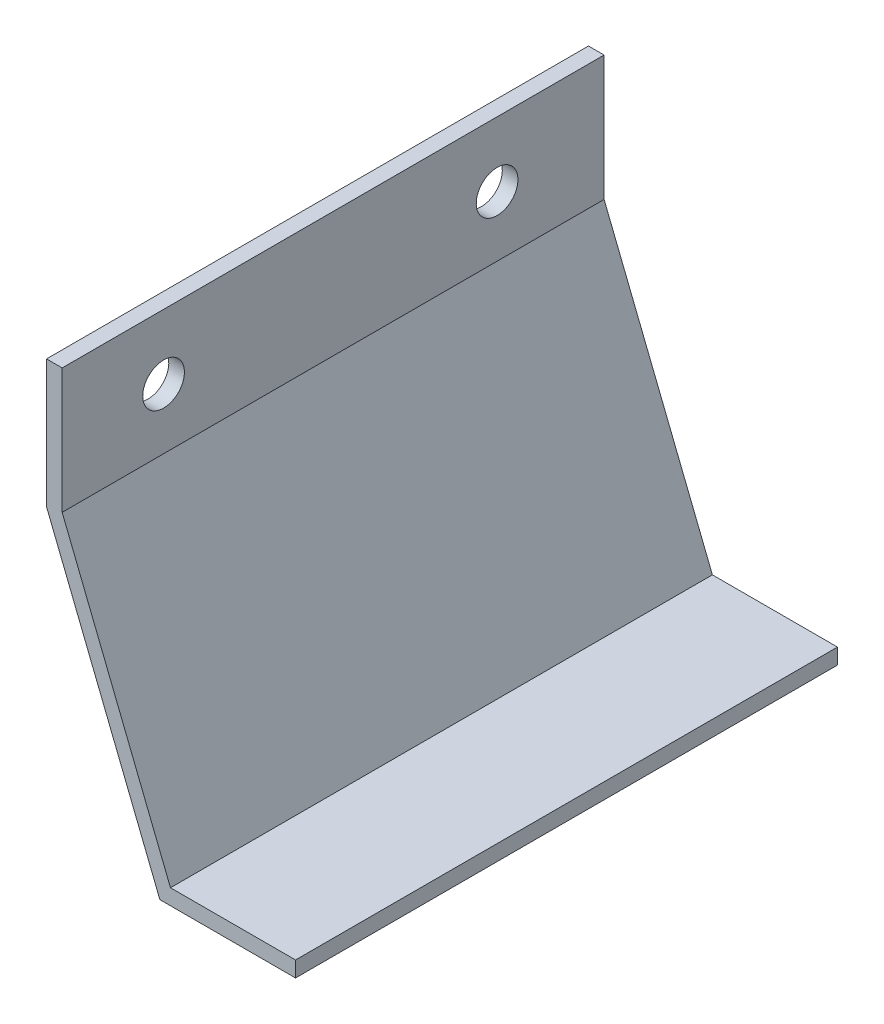
SolidWorks part; units mm, degrees
ref_plane "Front Plane" through (0, 0, 0) normal (0, 0, 1) x (1, 0, 0)
ref_plane "Top Plane" through (0, 0, 0) normal (0, 1, 0) x (1, 0, 0)
ref_plane "Right Plane" through (0, 0, 0) normal (1, 0, 0) x (0, 0, -1)
sketch "Sketch1" plane through (0, 0, 0) normal (0, 0, 1) x (1, 0, 0)
  line L0 (0, 120.65) -> (0, 82.55)
  line L1 (0, 82.55) -> (32.9956, 0)
  line L2 (32.9956, 0) -> (71.0956, 0)
  dimension "D1" = 38.1
  dimension "D2" = 38.1
  dimension "D3" = 82.55
  dimension "D4" = 88.9
extrude "Extrude-Thin1" add sketch "Sketch1" along normal blind 165.1 thin
sketch "Sketch2" plane through (0, 0, 0) normal (1, 0, 0) x (0, 0, -1)
  circle A0 centre (-134.2049, 100.9423) radius 6.35
  circle A1 centre (-32.6049, 100.9423) radius 6.35
  point P4 (0, 0)
  point P5 (-32.6049, 100.9423)
  dimension "D1" = 12.7
  dimension "D2" = 12.7
  dimension "D3" = 101.6
extrude "Cut-Extrude1" cut sketch "Sketch2" against normal through all
